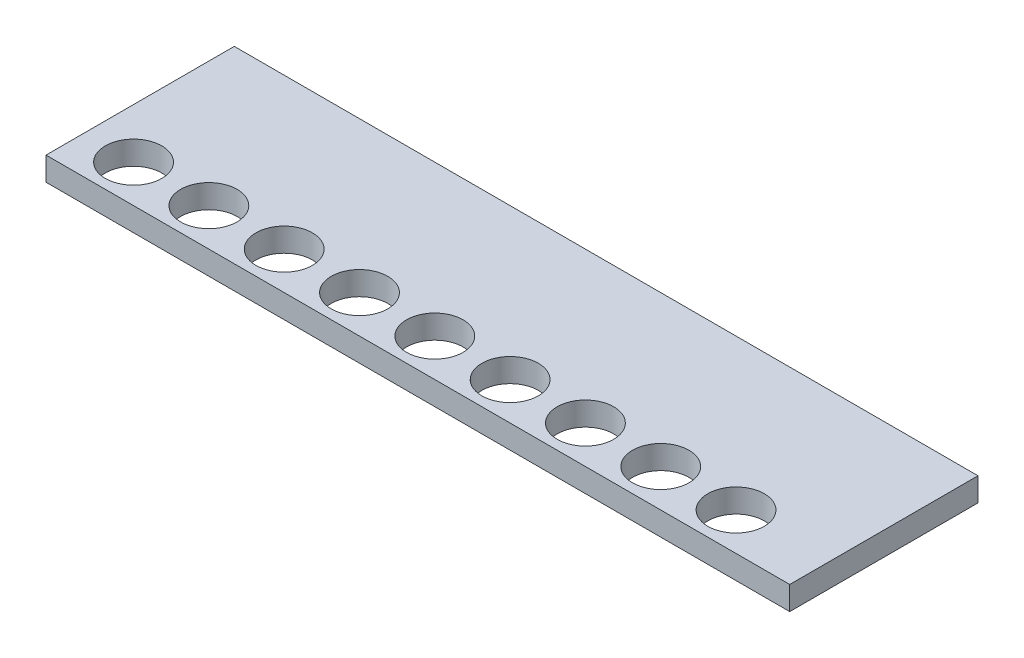
SolidWorks part; units mm, degrees
material "ABS"
ref_plane "Front Plane" through (0, 0, 0) normal (0, 0, 1) x (1, 0, 0)
ref_plane "Top Plane" through (0, 0, 0) normal (0, 1, 0) x (1, 0, 0)
ref_plane "Right Plane" through (0, 0, 0) normal (1, 0, 0) x (0, 0, -1)
sketch "Sketch2" plane through (0, 0, 0) normal (0, 1, 0) x (1, 0, 0)
  line L1 (-50.165, -12.7) -> (50.165, -12.7)
  line L2 (-50.165, -12.7) -> (-50.165, 12.7)
  line L3 (-50.165, 12.7) -> (50.165, 12.7)
  line L4 (50.165, -12.7) -> (50.165, 12.7)
  line L5 (-50.165, -12.7) -> (50.165, 12.7) construction
  line L6 (-50.165, 12.7) -> (50.165, -12.7) construction
  point P0 (0, 0)
  dimension "D1" = 100.33
  dimension "D2" = 25.4
extrude "Boss-Extrude1" add sketch "Sketch2" along normal blind 3.175
sketch "Sketch3" plane through (0, 3.175, 0) normal (0, 1, 0) x (1, 0, 0)
  line L0 (-50.165, -7.62) -> (50.165, -7.62) construction
  line L1 (-50.165, 12.7) -> (-50.165, -12.7) construction
  line L2 (50.165, -12.7) -> (50.165, 12.7) construction
  line L3 (-50.165, -12.7) -> (50.165, -12.7) construction
  circle A0 centre (-43.434, -7.62) radius 3.81
  circle A1 centre (-33.274, -7.62) radius 3.81
  circle A2 centre (-23.114, -7.62) radius 3.81
  circle A3 centre (-12.954, -7.62) radius 3.81
  circle A4 centre (-2.794, -7.62) radius 3.81
  circle A5 centre (7.366, -7.62) radius 3.81
  circle A6 centre (17.526, -7.62) radius 3.81
  circle A7 centre (27.686, -7.62) radius 3.81
  circle A8 centre (37.846, -7.62) radius 3.81
  dimension "D2" = 7.62
  dimension "D1" = 5.08
  dimension "D3" = 6.731
  dimension "D4" = 9
extrude "Cut-Extrude1" cut sketch "Sketch3" against normal through all
